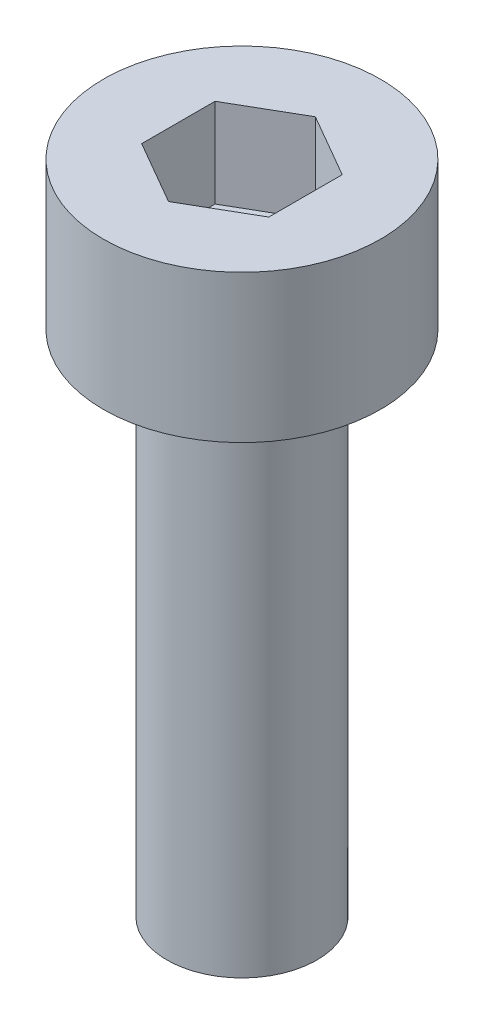
SolidWorks part; units mm, degrees
ref_plane "Front Plane" through (0, 0, 0) normal (0, 0, 1) x (1, 0, 0)
ref_plane "Top Plane" through (0, 0, 0) normal (0, 1, 0) x (1, 0, 0)
ref_plane "Right Plane" through (0, 0, 0) normal (1, 0, 0) x (0, 0, -1)
sketch "Sketch1" plane through (0, 0, 0) normal (0, 1, 0) x (1, 0, 0)
  circle A0 centre (0, 0) radius 2.725
  dimension "D1" = 5.45
extrude "Boss-Extrude1" add sketch "Sketch1" along normal blind 2.9
sketch "Sketch2" plane through (0, 0, 0) normal (0, -1, 0) x (1, 0, 0)
  circle A0 centre (0, 0) radius 1.475
  dimension "D1" = 2.95
extrude "Boss-Extrude2" add sketch "Sketch2" along normal blind 10
sketch "Sketch3" plane through (0, 2.9, 0) normal (0, 1, 0) x (1, 0, 0)
  line L1 (0, 1.4434) -> (-1.25, 0.7217)
  line L2 (-1.25, 0.7217) -> (-1.25, -0.7217)
  line L3 (-1.25, -0.7217) -> (0, -1.4434)
  line L4 (0, -1.4434) -> (1.25, -0.7217)
  line L5 (1.25, -0.7217) -> (1.25, 0.7217)
  line L6 (1.25, 0.7217) -> (0, 1.4434)
  circle A0 centre (0, 0) radius 1.25 construction
  dimension "D1" = 2.5
extrude "Cut-Extrude1" cut sketch "Sketch3" against normal blind 1.75
